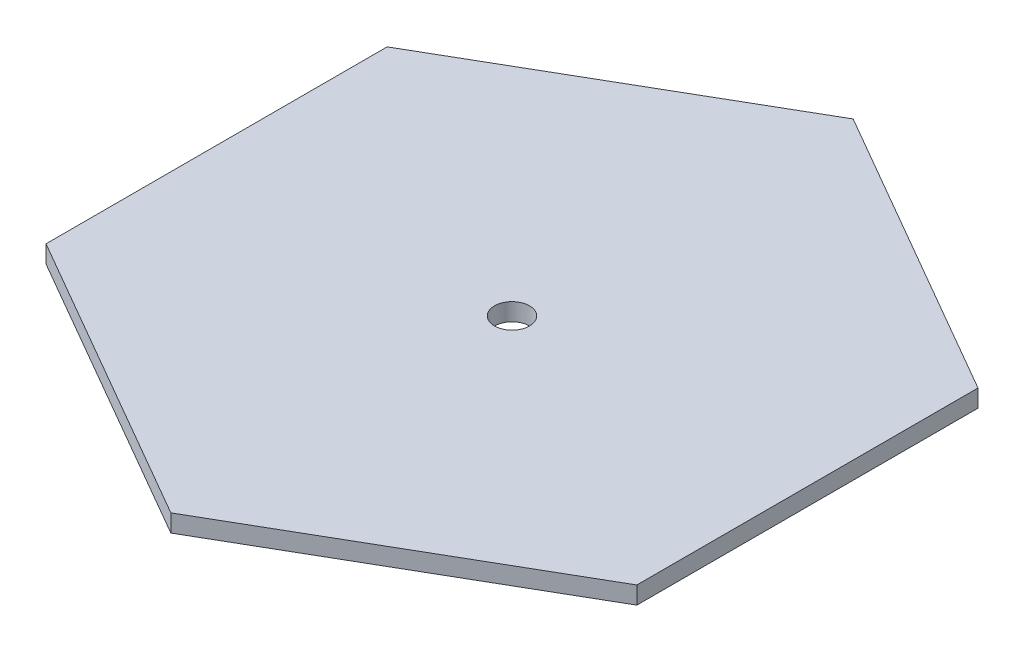
SolidWorks part; units mm, degrees
ref_plane "Front" through (0, 0, 0) normal (0, 0, 1) x (1, 0, 0)
ref_plane "Top" through (0, 0, 0) normal (0, 1, 0) x (1, 0, 0)
ref_plane "Right" through (0, 0, 0) normal (1, 0, 0) x (0, 0, -1)
sketch "Sketch1" plane through (0, 0, 0) normal (0, 1, 0) x (1, 0, 0)
  line L1 (33.775, 19.5) -> (0, 39)
  line L2 (0, 39) -> (-33.775, 19.5)
  line L3 (-33.775, 19.5) -> (-33.775, -19.5)
  line L4 (-33.775, -19.5) -> (0, -39)
  line L5 (0, -39) -> (33.775, -19.5)
  line L6 (33.775, -19.5) -> (33.775, 19.5)
  circle A0 centre (0, 0) radius 33.775 construction
  dimension "D1" = 78
extrude "Boss-Extrude1" add sketch "Sketch1" along normal blind 2
sketch "Sketch2" plane through (0, 2, 0) normal (0, 1, 0) x (1, 0, 0)
  circle A0 centre (0, 0) radius 2
  dimension "D1" = 4
extrude "Cut-Extrude1" cut sketch "Sketch2" against normal up to next
